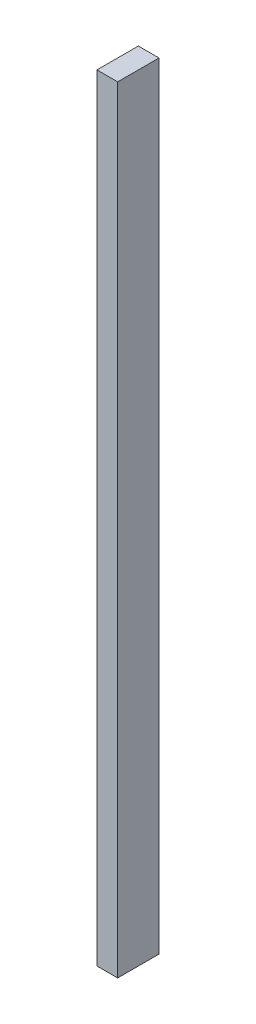
SolidWorks part; units mm, degrees
ref_plane "Front Plane" through (0, 0, 0) normal (0, 0, 1) x (1, 0, 0)
ref_plane "Top Plane" through (0, 0, 0) normal (0, 1, 0) x (1, 0, 0)
ref_plane "Right Plane" through (0, 0, 0) normal (1, 0, 0) x (0, 0, -1)
sketch "Sketch1" plane through (0, 0, 0) normal (0, 0, 1) x (1, 0, 0)
  line L1 (-52.3261, 3.2237) -> (-51.5261, 3.2237)
  line L2 (-52.3261, 3.2237) -> (-52.3261, -26.7763)
  line L3 (-52.3261, -26.7763) -> (-51.5261, -26.7763)
  line L4 (-51.5261, 3.2237) -> (-51.5261, -26.7763)
  dimension "D1" = 30
  dimension "D2" = 0.8
extrude "Boss-Extrude1" add sketch "Sketch1" along normal blind 1.6
